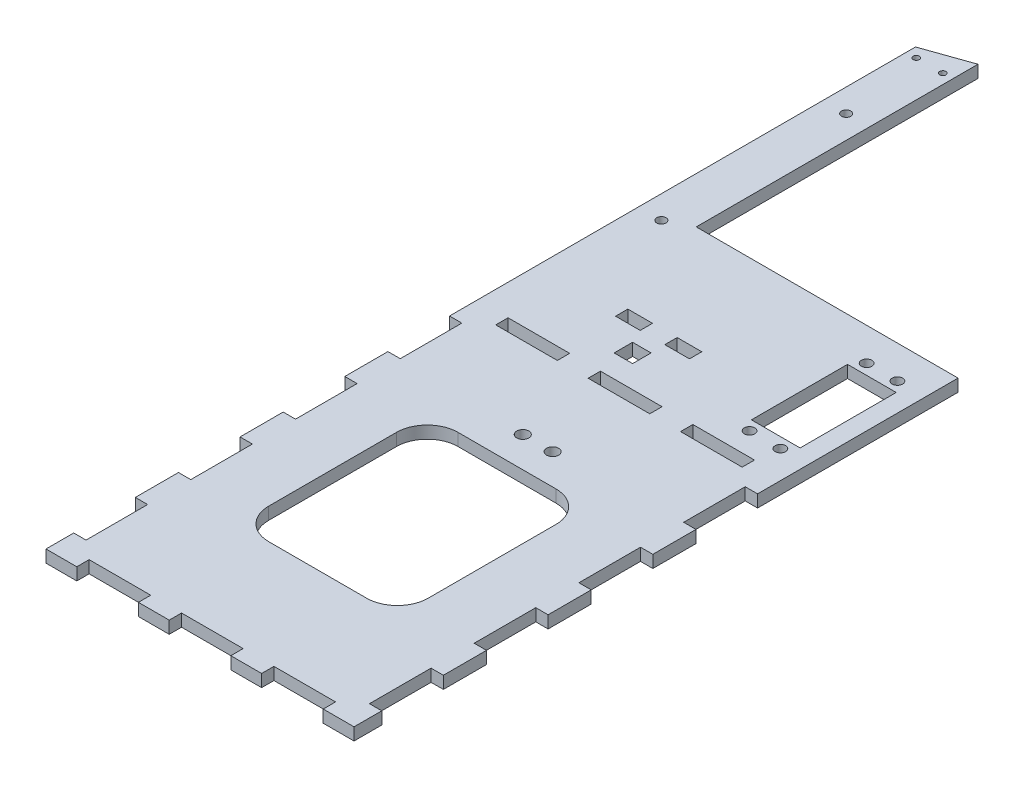
SolidWorks part; units mm, degrees
ref_plane "Front Plane" through (0, 0, 0) normal (0, 0, 1) x (1, 0, 0)
ref_plane "Top Plane" through (0, 0, 0) normal (0, 1, 0) x (1, 0, 0)
ref_plane "Right Plane" through (0, 0, 0) normal (1, 0, 0) x (0, 0, -1)
sketch "Sketch2" plane through (0, 0, 0) normal (0, 1, 0) x (1, 0, 0)
  line L0 (-19.05, -71.2393) -> (-19.05, -249.0393)
  line L1 (0, 0) -> (107.95, 0)
  line L2 (-19.05, -249.0393) -> (107.95, -249.0393)
  line L3 (107.95, -249.0393) -> (107.95, -60.96)
  line L4 (107.95, 0) -> (107.95, -60.96)
  line L5 (-19.05, -71.2393) -> (-19.05, 109.4501)
  line L6 (-19.05, 109.4501) -> (0, 116.1658)
  line L7 (0, 116.1658) -> (0, 97.4731)
  line L8 (0, 65.786) -> (0, 0)
  line L9 (0, 65.786) -> (0, 97.4731)
  dimension "D1" = 107.95
  dimension "D2" = 60.96
  dimension "D3" = 180.6894
  dimension "D4" = 180
  dimension "D5" = 127
  dimension "D7" = 90
  dimension "D8" = 90
  dimension "D9" = 177.8
extrude "Boss-Extrude1" add sketch "Sketch2" along normal blind 5.08
sketch "Sketch3" plane through (0, 5.08, 0) normal (0, 1, 0) x (1, 0, 0)
  line L0 (-19.05, -249.0393) -> (107.95, -249.0393) construction
  line L1 (80.264, -17.8917) -> (100.33, -17.8917)
  line L2 (80.264, -17.8917) -> (80.264, -57.5157)
  line L3 (80.264, -57.5157) -> (100.33, -57.5157)
  line L4 (100.33, -17.8917) -> (100.33, -57.5157)
  line L7 (107.95, -249.0393) -> (107.95, 0) construction
  dimension "D1" = 20.066
  dimension "D2" = 39.624
  dimension "D3" = 191.5236
  dimension "D4" = 7.62
extrude "Cut-Extrude1" cut sketch "Sketch3" against normal up to surface (5.08 mm away) up to face at (29.6333, 0, 45.4105)
sketch "Sketch4" plane through (0, 5.08, 0) normal (0, 1, 0) x (1, 0, 0)
  line L0 (80.264, -17.8917) -> (80.264, -57.5157) construction
  line L1 (100.33, -57.5157) -> (100.33, -17.8917) construction
  line L2 (100.33, -17.8917) -> (80.264, -17.8917) construction
  line L3 (80.264, -57.5157) -> (100.33, -57.5157) construction
  circle A0 centre (83.82, -13.5737) radius 2.159
  circle A1 centre (96.52, -13.5737) radius 2.159
  circle A2 centre (83.82, -61.8337) radius 2.159
  circle A3 centre (96.52, -61.8337) radius 2.159
  dimension "D1" = 4.318
  dimension "D3" = 3.556
  dimension "D6" = 12.7
  dimension "D7" = 3.81
  dimension "D2" = 12.7
  dimension "D4" = 3.81
  dimension "D5" = 4.318
  dimension "D8" = 4.318
  dimension "D9" = 4.318
extrude "Cut-Extrude2" cut sketch "Sketch4" against normal up to surface (5.08 mm away) up to face at (90.297, 0, 37.7037)
sketch "Sketch5" plane through (0, 5.08, 0) normal (0, 1, 0) x (1, 0, 0)
  line L0 (-19.05, 109.4501) -> (-19.05, -249.0393) construction
  line L1 (24.257, -122.4614) -> (64.6111, -122.4614)
  line L2 (11.557, -135.1614) -> (11.557, -187.8191)
  line L3 (24.257, -200.5191) -> (64.6111, -200.5191)
  line L4 (77.3111, -135.1614) -> (77.3111, -187.8191)
  line L5 (107.95, -249.0393) -> (107.95, 0) construction
  line L6 (107.95, 0) -> (0, 0) construction
  line L7 (-19.05, -249.0393) -> (107.95, -249.0393) construction
  arc A0 (77.3111, -135.1614) -> (64.6111, -122.4614) centre (64.6111, -135.1614) ccw
  arc A1 (64.6111, -200.5191) -> (77.3111, -187.8191) centre (64.6111, -187.8191) ccw
  arc A2 (11.557, -187.8191) -> (24.257, -200.5191) centre (24.257, -187.8191) ccw
  arc A3 (11.557, -135.1614) -> (24.257, -122.4614) centre (24.257, -135.1614) cw
  dimension "D2" = 12.7
  dimension "D1" = 30.607
  dimension "D3" = 30.6389
  dimension "D4" = 122.4614
  dimension "D5" = 48.5203
extrude "Cut-Extrude3" cut sketch "Sketch5" against normal up to surface (5.08 mm away) up to face at (96.52, 0, 63.9927)
sketch "Sketch6" plane through (0, 5.08, 0) normal (0, 1, 0) x (1, 0, 0)
  line L0 (107.95, -249.0393) -> (107.95, 0) construction
  line L1 (102.87, -237.6093) -> (107.95, -237.6093)
  line L2 (102.87, -237.6093) -> (102.87, -212.2093)
  line L3 (102.87, -212.2093) -> (107.95, -212.2093)
  line L4 (107.95, -237.6093) -> (107.95, -212.2093)
  line L5 (-19.05, -249.0393) -> (107.95, -249.0393) construction
  dimension "D1" = 5.08
  dimension "D2" = 11.43
  dimension "D3" = 25.4
extrude "Cut-Extrude4" cut sketch "Sketch6" against normal up to surface (5.08 mm away) up to face at (44.4341, 0, 161.4902)
sketch "Sketch7" plane through (0, 5.08, 0) normal (0, 1, 0) x (1, 0, 0)
  line L0 (107.95, -212.2093) -> (107.95, 0) construction
  line L1 (102.87, -194.4293) -> (107.95, -194.4293)
  line L2 (102.87, -194.4293) -> (102.87, -169.0293)
  line L3 (102.87, -169.0293) -> (107.95, -169.0293)
  line L4 (107.95, -194.4293) -> (107.95, -169.0293)
  line L5 (107.95, -212.2093) -> (102.87, -212.2093) construction
  dimension "D1" = 5.08
  dimension "D2" = 25.4
  dimension "D3" = 17.78
extrude "Cut-Extrude5" cut sketch "Sketch7" against normal up to surface (5.08 mm away) up to face at (44.4341, 0, 161.4902)
sketch "Sketch8" plane through (0, 5.08, 0) normal (0, 1, 0) x (1, 0, 0)
  line L0 (107.95, -169.0293) -> (107.95, 0) construction
  line L1 (102.87, -151.2493) -> (107.95, -151.2493)
  line L2 (102.87, -151.2493) -> (102.87, -125.8493)
  line L3 (102.87, -125.8493) -> (107.95, -125.8493)
  line L4 (107.95, -151.2493) -> (107.95, -125.8493)
  line L5 (102.87, -108.0693) -> (107.95, -108.0693)
  line L6 (102.87, -108.0693) -> (102.87, -82.6693)
  line L7 (102.87, -82.6693) -> (107.95, -82.6693)
  line L8 (107.95, -108.0693) -> (107.95, -82.6693)
  line L9 (107.95, -169.0293) -> (102.87, -169.0293) construction
  dimension "D1" = 5.08
  dimension "D2" = 17.78
  dimension "D3" = 5.08
  dimension "D4" = 25.4
  dimension "D5" = 17.78
  dimension "D6" = 25.4
extrude "Cut-Extrude6" cut sketch "Sketch8" against normal up to surface (5.08 mm away) up to face at (44.4341, 0, 161.4902)
sketch "Sketch9" plane through (0, 5.08, 0) normal (0, 1, 0) x (1, 0, 0)
  line L0 (-19.05, 109.4501) -> (-19.05, -249.0393) construction
  line L1 (-19.05, -237.6093) -> (-13.97, -237.6093)
  line L2 (-19.05, -237.6093) -> (-19.05, -212.2093)
  line L3 (-19.05, -212.2093) -> (-13.97, -212.2093)
  line L4 (-13.97, -237.6093) -> (-13.97, -212.2093)
  line L5 (-19.05, -194.4293) -> (-13.97, -194.4293)
  line L6 (-19.05, -194.4293) -> (-19.05, -169.0293)
  line L7 (-19.05, -169.0293) -> (-13.97, -169.0293)
  line L8 (-13.97, -194.4293) -> (-13.97, -169.0293)
  line L9 (-19.05, -151.2493) -> (-13.97, -151.2493)
  line L10 (-19.05, -151.2493) -> (-19.05, -125.8493)
  line L11 (-19.05, -125.8493) -> (-13.97, -125.8493)
  line L12 (-13.97, -151.2493) -> (-13.97, -125.8493)
  line L13 (-19.05, -108.0693) -> (-13.97, -108.0693)
  line L14 (-19.05, -108.0693) -> (-19.05, -82.6693)
  line L15 (-19.05, -82.6693) -> (-13.97, -82.6693)
  line L16 (-13.97, -108.0693) -> (-13.97, -82.6693)
  line L17 (102.87, -237.6093) -> (107.95, -237.6093) construction
  line L18 (107.95, -212.2093) -> (102.87, -212.2093) construction
  line L19 (102.87, -194.4293) -> (107.95, -194.4293) construction
  line L20 (107.95, -169.0293) -> (102.87, -169.0293) construction
  line L21 (102.87, -151.2493) -> (107.95, -151.2493) construction
  line L22 (107.95, -125.8493) -> (102.87, -125.8493) construction
  line L23 (102.87, -108.0693) -> (107.95, -108.0693) construction
  line L24 (107.95, -82.6693) -> (102.87, -82.6693) construction
  dimension "D1" = 5.08
  dimension "D2" = 5.08
  dimension "D3" = 5.08
  dimension "D4" = 5.08
  dimension "D5" = 0
  dimension "D6" = 0
  dimension "D7" = 0
  dimension "D8" = 0
  dimension "D9" = 0
  dimension "D10" = 0
  dimension "D11" = 0
  dimension "D12" = 0
extrude "Cut-Extrude7" cut sketch "Sketch9" against normal up to surface (5.08 mm away) up to face at (44.4341, 0, 161.4902)
sketch "Sketch10" plane through (0, 5.08, 0) normal (0, 1, 0) x (1, 0, 0)
  line L0 (-19.05, 109.4501) -> (-19.05, -82.6693) construction
  line L1 (-6.35, -71.2393) -> (19.05, -71.2393)
  line L2 (-6.35, -71.2393) -> (-6.35, -76.3193)
  line L3 (-6.35, -76.3193) -> (19.05, -76.3193)
  line L4 (19.05, -71.2393) -> (19.05, -76.3193)
  line L5 (-13.97, -82.6693) -> (-19.05, -82.6693) construction
  line L8 (31.75, -71.2393) -> (57.15, -71.2393)
  line L9 (31.75, -71.2393) -> (31.75, -76.3193)
  line L10 (31.75, -76.3193) -> (57.15, -76.3193)
  line L11 (57.15, -71.2393) -> (57.15, -76.3193)
  line L12 (69.85, -71.2393) -> (95.25, -71.2393)
  line L13 (69.85, -71.2393) -> (69.85, -76.3193)
  line L14 (69.85, -76.3193) -> (95.25, -76.3193)
  line L15 (95.25, -71.2393) -> (95.25, -76.3193)
  dimension "D1" = 5.08
  dimension "D2" = 12.7
  dimension "D3" = 6.35
  dimension "D4" = 25.4
  dimension "D5" = 25.4
  dimension "D6" = 12.7
  dimension "D7" = 0
  dimension "D8" = 5.08
  dimension "D9" = 5.08
  dimension "D10" = 0
  dimension "D11" = 25.4
  dimension "D12" = 12.7
extrude "Cut-Extrude8" cut sketch "Sketch10" against normal up to surface (5.08 mm away) up to face at (44.4341, 0, 161.4902)
sketch "Sketch11" plane through (0, 5.08, 0) normal (0, 1, 0) x (1, 0, 0)
  line L0 (-19.05, -249.0393) -> (107.95, -249.0393) construction
  line L1 (-6.35, -243.9593) -> (19.05, -243.9593)
  line L2 (-6.35, -243.9593) -> (-6.35, -249.0393)
  line L3 (-6.35, -249.0393) -> (19.05, -249.0393)
  line L4 (19.05, -243.9593) -> (19.05, -249.0393)
  line L5 (-6.35, -71.2393) -> (-6.35, -76.3193) construction
  line L6 (19.05, -76.3193) -> (19.05, -71.2393) construction
  line L7 (31.75, -71.2393) -> (31.75, -76.3193) construction
  line L8 (31.75, -243.9593) -> (57.15, -243.9593)
  line L9 (31.75, -243.9593) -> (31.75, -249.0393)
  line L10 (31.75, -249.0393) -> (57.15, -249.0393)
  line L11 (57.15, -243.9593) -> (57.15, -249.0393)
  line L12 (69.85, -243.9593) -> (95.25, -243.9593)
  line L13 (69.85, -243.9593) -> (69.85, -249.0393)
  line L14 (69.85, -249.0393) -> (95.25, -249.0393)
  line L15 (95.25, -243.9593) -> (95.25, -249.0393)
  line L16 (57.15, -76.3193) -> (57.15, -71.2393) construction
  line L17 (69.85, -71.2393) -> (69.85, -76.3193) construction
  line L18 (95.25, -76.3193) -> (95.25, -71.2393) construction
  dimension "D1" = 5.08
  dimension "D2" = 0
  dimension "D3" = 0
  dimension "D4" = 5.08
  dimension "D5" = 5.08
  dimension "D6" = 0
  dimension "D7" = 0
  dimension "D8" = 0
  dimension "D9" = 0
extrude "Cut-Extrude9" cut sketch "Sketch11" against normal up to surface (5.08 mm away) up to face at (82.55, 0, 73.7793)
sketch "Sketch12" plane through (0, 5.08, 0) normal (0, 1, 0) x (1, 0, 0)
  line L0 (-19.05, 109.4501) -> (-19.05, -82.6693) construction
  line L1 (0, 0) -> (0, 116.1658) construction
  circle A0 centre (-14.998, 105.7009) radius 1.27
  circle A1 centre (-4.064, 105.7009) radius 1.27
  dimension "D1" = 2.54
  dimension "D3" = 4.064
  dimension "D2" = 4.052
extrude "Cut-Extrude10" cut sketch "Sketch12" against normal up to surface (5.08 mm away) up to face at (82.55, 0, 73.7793)
sketch "Sketch13" plane through (0, 5.08, 0) normal (0, 1, 0) x (1, 0, 0)
  line L0 (-19.05, 109.4501) -> (-19.05, -82.6693) construction
  line L1 (15.24, -43.4347) -> (25.4, -43.4347)
  line L2 (15.24, -43.4347) -> (15.24, -48.5147)
  line L3 (15.24, -48.5147) -> (25.4, -48.5147)
  line L4 (25.4, -43.4347) -> (25.4, -48.5147)
  line L5 (35.56, -43.4347) -> (45.72, -43.4347)
  line L6 (35.56, -43.4347) -> (35.56, -48.5147)
  line L7 (35.56, -48.5147) -> (45.72, -48.5147)
  line L8 (45.72, -43.4347) -> (45.72, -48.5147)
  line L10 (80.264, -57.5157) -> (80.264, -17.8917) construction
  dimension "D1" = 5.08
  dimension "D2" = 5.08
  dimension "D3" = 10.16
  dimension "D4" = 10.16
  dimension "D5" = 10.16
  dimension "D6" = 34.29
  dimension "D7" = 34.544
extrude "Cut-Extrude11" cut sketch "Sketch13" against normal up to surface (5.08 mm away) up to face at (-4.064, 0, -104.4309)
sketch "Sketch14" plane through (0, 5.08, 0) normal (0, 1, 0) x (1, 0, 0)
  line L0 (35.56, -48.5147) -> (45.72, -48.5147) construction
  line L1 (28.067, -54.3098) -> (35.687, -54.3098)
  line L2 (28.067, -54.3098) -> (28.067, -61.9298)
  line L3 (28.067, -61.9298) -> (35.687, -61.9298)
  line L4 (35.687, -54.3098) -> (35.687, -61.9298)
  line L6 (-19.05, 109.4501) -> (-19.05, -82.6693) construction
  dimension "D1" = 5.7951
  dimension "D2" = 7.62
  dimension "D3" = 7.62
  dimension "D4" = 47.117
extrude "Cut-Extrude12" cut sketch "Sketch14" against normal up to surface (5.08 mm away) up to face at (40.64, 0, 45.9747)
sketch "Sketch15" plane through (0, 5.08, 0) normal (0, 1, 0) x (1, 0, 0)
  line L1 (0, 0) -> (0, 116.1658) construction
  line L2 (-19.05, 109.4501) -> (-19.05, -82.6693) construction
  circle A0 centre (-9.5377, 71.3501) radius 1.905
  circle A1 centre (-9.5377, -4.8499) radius 1.905
  dimension "D1" = 3.81
  dimension "D2" = 76.2
  dimension "D3" = 38.1
  dimension "D4" = 9.5377
  dimension "D5" = 9.5123
extrude "Cut-Extrude13" cut sketch "Sketch15" against normal up to surface (5.08 mm away) up to face at (31.877, 0, 58.1198)
sketch "Sketch16" plane through (0, 5.08, 0) normal (0, 1, 0) x (1, 0, 0)
  line L0 (107.95, -125.8493) -> (107.95, -108.0693) construction
  line L1 (-19.05, -108.0693) -> (-19.05, -125.8493) construction
  circle A0 centre (38.354, -109.8699) radius 2.4955
  circle A1 centre (50.6586, -109.8699) radius 2.4955
  dimension "D1" = 4.9911
  dimension "D2" = 57.2914
  dimension "D3" = 57.404
extrude "Cut-Extrude14" cut sketch "Sketch16" against normal up to surface (5.08 mm away) up to face at (-9.5377, 0, 6.7549)
